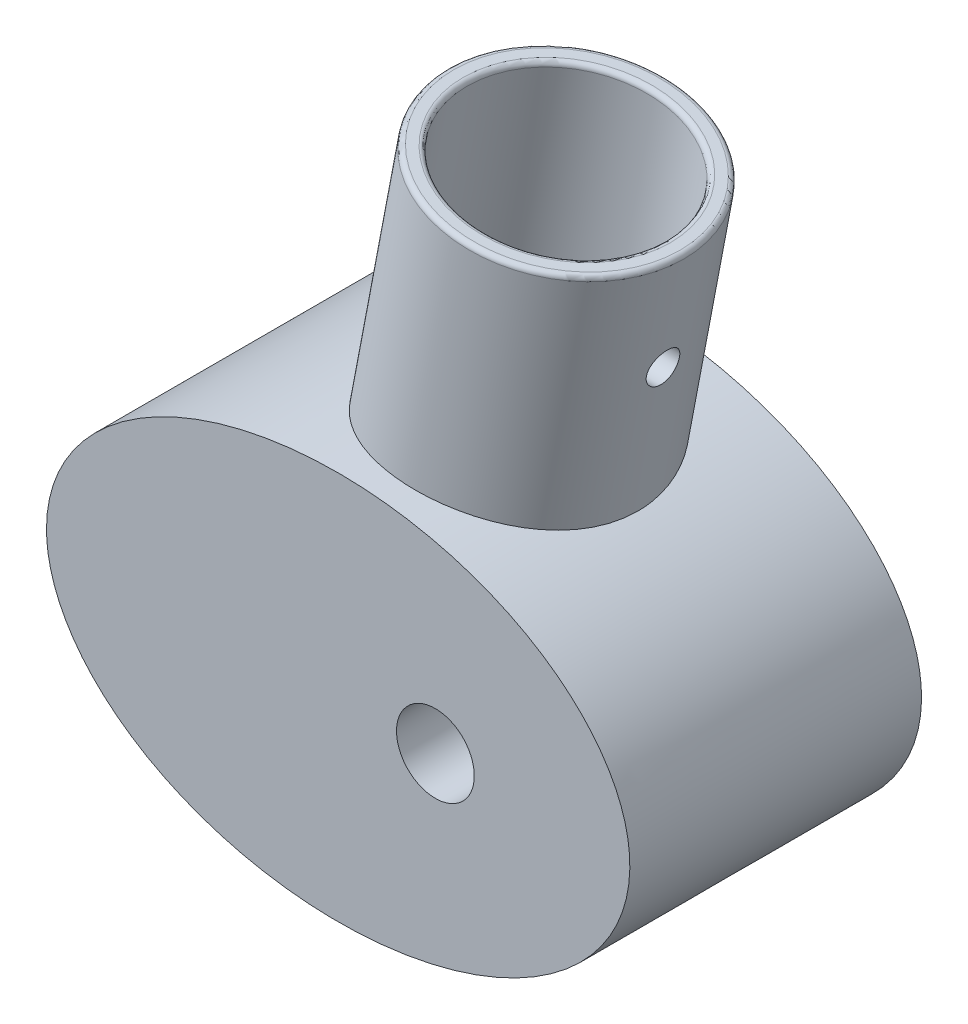
SolidWorks part; units mm, degrees
ref_plane "Front Plane" through (0, 0, 0) normal (0, 0, 1) x (1, 0, 0)
ref_plane "Top Plane" through (0, 0, 0) normal (0, 1, 0) x (1, 0, 0)
ref_plane "Right Plane" through (0, 0, 0) normal (1, 0, 0) x (0, 0, -1)
sketch "Sketch2" plane through (0, 0, 0) normal (0, 0, 1) x (1, 0, 0)
  line L102 (-3.3983, 10.2) -> (7.0395, 10.2) construction
  line L103 (7.0395, 10.2) -> (29.1, 10.2) construction
  line L104 (30.1, 9.2) -> (30.1, 0.75) construction
  line L105 (31.7, 0.75) -> (30.1, 0.75) construction
  line L106 (31.7, 0.75) -> (35.9, 0.75) construction
  line L107 (35.9, 0.75) -> (35.9, -0.75) construction
  line L108 (35.9, -0.75) -> (30.1, -0.75) construction
  line L109 (30.1, -0.75) -> (30.1, -9.2) construction
  line L110 (29.1, -10.2) -> (7.0395, -10.2) construction
  line L111 (7.0395, -10.2) -> (-3.3983, -10.2) construction
  line L112 (-3.3983, -10.2) -> (-9.1, -10.2) construction
  line L113 (-11.7, -0.75) -> (-10.1, -0.75) construction
  line L114 (-11.7, -0.75) -> (-15.9, -0.75) construction
  line L115 (-15.9, -0.75) -> (-15.9, 0.75) construction
  line L116 (-15.9, 0.75) -> (-11.7, 0.75) construction
  line L117 (-10.1, 0.75) -> (-11.7, 0.75) construction
  line L118 (-10.1, -9.2) -> (-10.1, -0.75) construction
  line L119 (-10.1, 0.75) -> (-10.1, 9.2) construction
  line L120 (-9.1, 10.2) -> (-3.3983, 10.2) construction
  line L121 (-3.3983, 10.6) -> (7.0395, 10.6)
  line L122 (7.0395, 10.6) -> (29.1, 10.6)
  line L123 (30.5, 9.2) -> (30.5, 1.15)
  line L124 (31.7, 1.15) -> (30.5, 1.15)
  line L125 (31.7, 1.15) -> (36.3, 1.15)
  line L126 (36.3, 1.15) -> (36.3, -1.15)
  line L127 (36.3, -1.15) -> (30.5, -1.15)
  line L128 (30.5, -1.15) -> (30.5, -9.2)
  line L129 (29.1, -10.6) -> (7.0395, -10.6)
  line L130 (7.0395, -10.6) -> (-3.3983, -10.6)
  line L131 (-3.3983, -10.6) -> (-9.1, -10.6)
  line L132 (-10.5, -9.2) -> (-10.5, -1.15)
  line L133 (-11.7, -1.15) -> (-10.5, -1.15)
  line L134 (-11.7, -1.15) -> (-16.3, -1.15)
  line L135 (-16.3, -1.15) -> (-16.3, 1.15)
  line L136 (-16.3, 1.15) -> (-11.7, 1.15)
  line L137 (-10.5, 1.15) -> (-11.7, 1.15)
  line L138 (-10.5, 1.15) -> (-10.5, 9.2)
  line L139 (-9.1, 10.6) -> (-3.3983, 10.6)
  arc A20 (30.1, 9.2) -> (29.1, 10.2) centre (29.1, 9.2) ccw construction
  arc A21 (29.1, -10.2) -> (30.1, -9.2) centre (29.1, -9.2) ccw construction
  arc A22 (-10.1, -9.2) -> (-9.1, -10.2) centre (-9.1, -9.2) ccw construction
  arc A23 (-9.1, 10.2) -> (-10.1, 9.2) centre (-9.1, 9.2) ccw construction
  arc A24 (30.5, 9.2) -> (29.1, 10.6) centre (29.1, 9.2) ccw
  arc A25 (29.1, -10.6) -> (30.5, -9.2) centre (29.1, -9.2) ccw
  arc A26 (-10.5, -9.2) -> (-9.1, -10.6) centre (-9.1, -9.2) ccw
  arc A27 (-9.1, 10.6) -> (-10.5, 9.2) centre (-9.1, 9.2) ccw
  ellipse E0 centre (10, 0) end of major axis (40, 0) minor radius 20
  dimension "D2" = 60
  dimension "D3" = 40
  dimension "D4" = 10
  dimension "D1" = 0.4
extrude "Boss-Extrude1" add sketch "Sketch2" along normal blind 30
sketch "Sketch3" plane through (0, 0, 0) normal (0, 0, -1) x (-1, 0, 0)
  arc A0 (-36.8729, -5.875) -> (-36.8729, -4.125) centre (-34.8, -5) ccw construction
  arc A1 (-36.8729, 4.125) -> (-36.8729, 5.875) centre (-34.8, 5) ccw construction
  arc A2 (16.8729, 5.875) -> (16.8729, 4.125) centre (14.8, 5) ccw construction
  arc A3 (16.8729, -4.125) -> (16.8729, -5.875) centre (14.8, -5) ccw construction
  arc A4 (-36.8729, -5.875) -> (-36.8729, -4.125) centre (-34.8, -5) ccw construction
  arc A5 (-36.8729, 4.125) -> (-36.8729, 5.875) centre (-34.8, 5) ccw construction
  arc A6 (16.8729, 5.875) -> (16.8729, 4.125) centre (14.8, 5) ccw construction
  arc A7 (16.8729, -4.125) -> (16.8729, -5.875) centre (14.8, -5) ccw construction
  arc A8 (16.8729, -5.875) -> (16.8729, -4.125) centre (14.8, -5) ccw construction
  arc A9 (16.8729, 4.125) -> (16.8729, 5.875) centre (14.8, 5) ccw construction
  arc A10 (-36.8729, 5.875) -> (-36.8729, 4.125) centre (-34.8, 5) ccw construction
  arc A11 (-36.8729, -4.125) -> (-36.8729, -5.875) centre (-34.8, -5) ccw construction
  arc A12 (-35.9516, -5.4861) -> (-35.9516, -4.5139) centre (-34.8, -5) ccw
  arc A13 (-35.9516, -4.5139) -> (-35.9516, -5.4861) centre (-34.8, -5) ccw
  arc A14 (-35.9516, 4.5139) -> (-35.9516, 5.4861) centre (-34.8, 5) ccw
  arc A15 (-35.9516, 5.4861) -> (-35.9516, 4.5139) centre (-34.8, 5) ccw
  arc A16 (15.9516, 5.4861) -> (15.9516, 4.5139) centre (14.8, 5) ccw
  arc A17 (15.9516, 4.5139) -> (15.9516, 5.4861) centre (14.8, 5) ccw
  arc A18 (15.9516, -4.5139) -> (15.9516, -5.4861) centre (14.8, -5) ccw
  arc A19 (15.9516, -5.4861) -> (15.9516, -4.5139) centre (14.8, -5) ccw
  dimension "D1" = 1.25
extrude "Cut-Extrude1" cut sketch "Sketch3" against normal blind 3
ref_plane "Plane3" through (10, 0, 0) normal (1, 0, 0) x (0, 0, -1)
sketch "Sketch16" plane through (10, 0, 0) normal (1, 0, 0) x (0, 0, -1)
  line L0 (0, 0) -> (50000, 0) construction
ref_plane "Plane6" through (9.648, 1.8427, 0) normal (-0.9822, -0.1876, 0) x (0, 0, -1)
sketch "Sketch6" plane through (11.1721, -6.137, 0) normal (-0.9822, -0.1876, 0) x (-0.1876, 0.9822, 0)
  line L1 (26.6831, 0) -> (-14.1873, 0) construction
  line L3 (-14.1873, -30) -> (26.6831, -30) construction
  line L7 (26.6831, -15) -> (51.6831, -15)
  line L8 (26.6831, 0) -> (-14.1873, 0) construction
  line L9 (-14.1873, -30) -> (26.6831, -30) construction
  line L10 (26.6831, 0) -> (26.6831, -30) construction
  dimension "D1" = 25
ref_plane "Plane1" through (1.4762, 44.6285, 15) normal (-0.1876, 0.9822, 0) x (0.9822, 0.1876, 0)
sketch "Sketch7" plane through (1.4762, 44.6285, 15) normal (-0.1876, 0.9822, 0) x (0.9822, 0.1876, 0)
  circle A0 centre (0, 0) radius 10.35
  circle A1 centre (0, 0) radius 12.35
  point P12 (0, 0)
  dimension "D1" = 20.7
  dimension "D2" = 2
extrude "Boss-Extrude2" add sketch "Sketch7" against normal up to body
sketch "Sketch8" plane through (0, 0, 30) normal (0, 0, 1) x (1, 0, 0)
  line L0 (10, 0) -> (10, -3.4904) construction
  ellipse E0 centre (10, 0) end of major axis (40, 0) minor radius 20 construction
  ellipse E1 centre (10, 0) end of major axis (40, 0) minor radius 20
extrude "Boss-Extrude4" add sketch "Sketch8" against normal up to surface (7.4 mm away)
sketch "Sketch12" plane through (10, -10, 0) normal (-1, 0, 0) x (0, 1, 0)
  line L6 (30, -30) -> (30, 0) construction
  line L7 (30, -15) -> (52.3116, -15) construction
  circle A0 centre (41.1558, -15) radius 1.7
  ellipse E0 centre (54.6285, -15) end of major axis (54.6285, -27.35) minor radius 2.3169 construction
  dimension "D1" = 3.4
extrude "Cut-Extrude3" cut sketch "Sketch12" against normal through all both and the other way through all
sketch "Sketch15" [suppressed] plane through (10, 0, 0) normal (1, 0, 0) x (0, 0, -1)
  line L0 (0, 0) -> (50000, 0) construction
  line L1 (0, -20) -> (0, 20) construction
  point P4 (0, 0)
ref_plane "Plane4" [suppressed] through (9.4211, -2.3354, 0) normal (0.9706, -0.2406, 0) x (0, 0, -1)
sketch "Sketch9" [suppressed] plane through (12.5635, 10.3412, 0) normal (0.9706, -0.2406, 0) x (-0.2406, -0.9706, 0)
  line L0 (31.3652, -30) -> (31.3652, 0) construction
  line L1 (31.3652, -30) -> (31.3652, 0) construction
  line L2 (31.3652, -15) -> (55.6745, -9.1639)
  dimension "D1" = 25
  dimension "D2" = 13.5
ref_plane "Plane2" [suppressed] through (-0.8323, -43.6977, 9.1639) normal (-0.234, -0.9438, -0.2334) x (-0.4258, 0.3153, -0.8481)
sketch "Sketch10" [suppressed] plane through (-0.8323, -43.6977, 9.1639) normal (-0.234, -0.9438, -0.2334) x (-0.4258, 0.3153, -0.8481)
  line L0 (-12.7213, -7.1349) -> (12.7213, 7.1349) construction
  circle A0 centre (0, 0) radius 10.35
  circle A1 centre (0, 0) radius 12.35
  dimension "D1" = 20.7
  dimension "D2" = 2
extrude "Boss-Extrude5" [suppressed] add sketch "Sketch10" against normal up to surface (28.1469 mm away)
sketch "Sketch11" [suppressed] plane through (12.5635, 10.3412, 0) normal (0.9706, -0.2406, 0) x (-0.2406, -0.9706, 0)
  line L2 (31.3652, 0) -> (31.3652, -30) construction
  line L3 (31.3652, -15) -> (55.6745, -9.1639) construction
  line L4 (58.0906, -19.2279) -> (53.2583, 0.9002) construction
  circle A1 centre (43.5198, -12.0819) radius 1.7
  dimension "D1" = 3.4
extrude "Cut-Extrude2" [suppressed] cut sketch "Sketch11" against normal through all both and the other way through all
sketch "Sketch13" plane through (0, 0, 30) normal (0, 0, 1) x (1, 0, 0)
  circle A0 centre (0, 0) radius 4
  dimension "D1" = 8
extrude "Cut-Extrude4" cut sketch "Sketch13" against normal through all both and the other way through all
sketch "Sketch14" [suppressed] plane through (0, 0, 30) normal (0, 0, 1) x (1, 0, 0)
  circle A1 centre (20, 0) radius 4
  ellipse E3 centre (10, 0) end of major axis (40, 0) minor radius 20
  ellipse E4 centre (10, 0) end of major axis (40, 0) minor radius 20
  dimension "D1" = 8
  dimension "D3" = 10
  dimension "D2" = 0
extrude "Cut-Extrude5" [suppressed] cut sketch "Sketch14" against normal through all both and the other way through all contours A1
ref_plane "Plane5" through (-25, 0, 0) normal (1, 0, 0) x (0, 0, -1)
mirror "Mirror1" about plane through (-25, 0, 0) normal (1, 0, 0) of bodies 112 113
delete or keep bodies "Body-Delete/Keep 1" type delete bodies bodies 112
fillet "Fillet1" [suppressed] radius 0.5
fillet "Fillet2" [suppressed] radius 0.5
fillet "Fillet3" [suppressed] radius 0.5
fillet "Fillet4" radius 0.5 2 edges at (-39.3454, 42.3116, 15) (-41.3099, 42.6868, 15)
